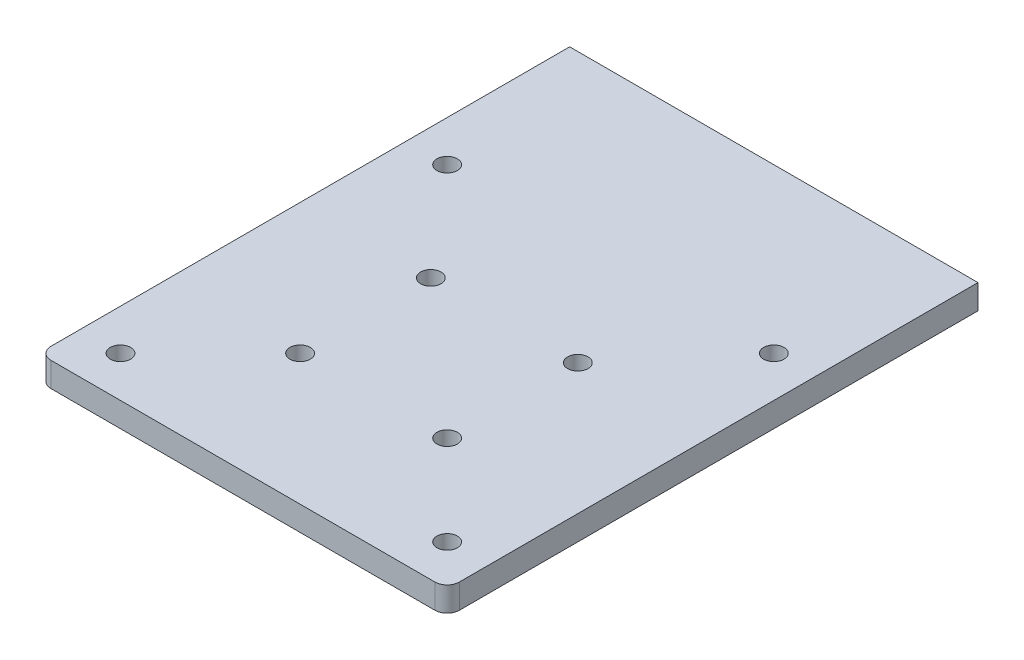
SolidWorks part; units mm, degrees
ref_plane "Front Plane" through (0, 0, 0) normal (0, 0, 1) x (1, 0, 0)
ref_plane "Top Plane" through (0, 0, 0) normal (0, 1, 0) x (1, 0, 0)
ref_plane "Right Plane" through (0, 0, 0) normal (1, 0, 0) x (0, 0, -1)
sketch "Sketch1" plane through (0, 0, 0) normal (0, 1, 0) x (1, 0, 0)
  line L1 (-10, 120) -> (90, 120)
  line L2 (-10, 120) -> (-10, -10)
  line L3 (-10, -10) -> (90, -10)
  line L4 (90, 120) -> (90, -10)
  circle A0 centre (0, 0) radius 2.5
  circle A1 centre (80, 0) radius 2.5
  circle A2 centre (0, 80) radius 2.5
  circle A3 centre (80, 80) radius 2.5
  circle A4 centre (0, 32) radius 2.5 [skipped]
  circle A5 centre (80, 32) radius 2.5 [skipped]
  circle A6 centre (22, 22) radius 2.5
  circle A7 centre (58, 22) radius 2.5
  circle A8 centre (22, 54) radius 2.5
  circle A9 centre (58, 54) radius 2.5
  dimension "D1" = 5
  dimension "D9" = 5
  dimension "D10" = 5
  dimension "D12" = 10
  dimension "D13" = 130
  dimension "D14" = 10
  dimension "D15" = 5
  dimension "D16" = 5
  dimension "D17" = 5
  dimension "D18" = 5
  dimension "D22" = 36
  dimension "D21" = 32
  dimension "D23" = 32
  dimension "D24" = 32
  dimension "D8" = 90
  dimension "D11" = 90
  dimension "D4" = 10
  dimension "D5" = 10
  dimension "D6" = 10
  dimension "D7" = 100
  dimension "D19" = 32
  dimension "D20" = 36
  dimension "D2" = 2
  dimension "D3" = 2
extrude "Boss-Extrude1" add sketch "Sketch1" along normal blind 6
fillet "Fillet1" radius 3 2 edges at (-10, 3, 10) (90, 3, 10)
scale "Scale1" scale about centroid uniform scaling yes scale factor 7.5
